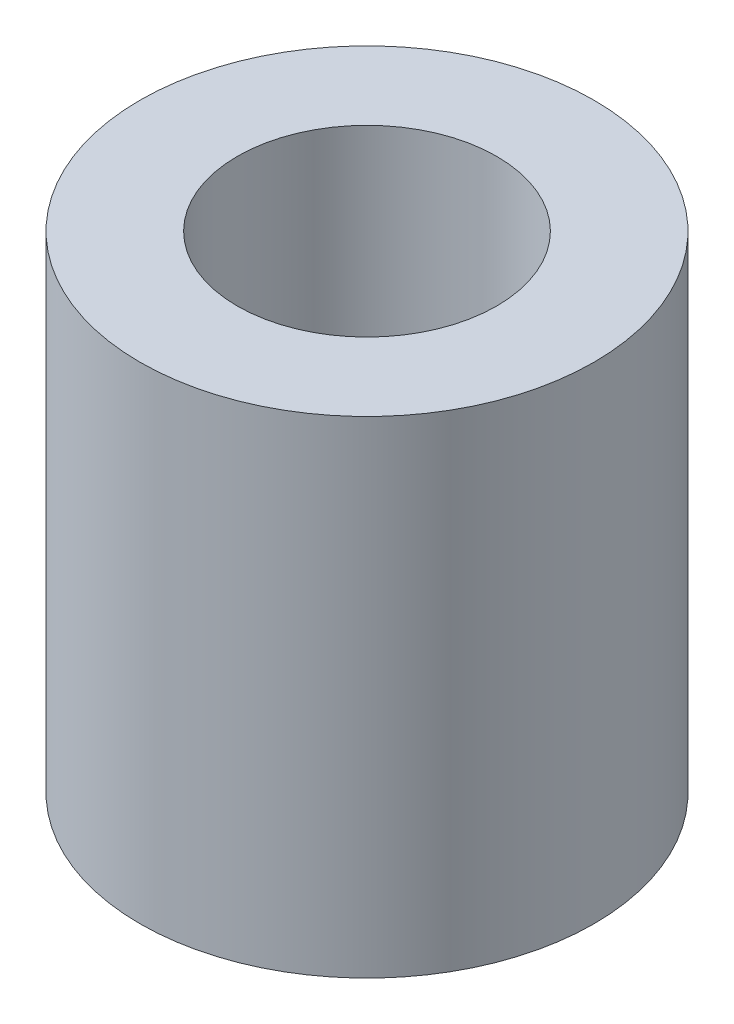
SolidWorks part; units mm, degrees
ref_plane "Front Plane" through (0, 0, 0) normal (0, 0, 1) x (1, 0, 0)
ref_plane "Top Plane" through (0, 0, 0) normal (0, 1, 0) x (1, 0, 0)
ref_plane "Right Plane" through (0, 0, 0) normal (1, 0, 0) x (0, 0, -1)
sketch "Sketch1" plane through (0, 0, 0) normal (0, 1, 0) x (1, 0, 0)
  circle A0 centre (0, 0) radius 4.445
  circle A1 centre (0, 0) radius 2.54
  dimension "D1" = 5.08
  dimension "D2" = 8.89
extrude "Boss-Extrude1" add sketch "Sketch1" along normal blind 9.525
